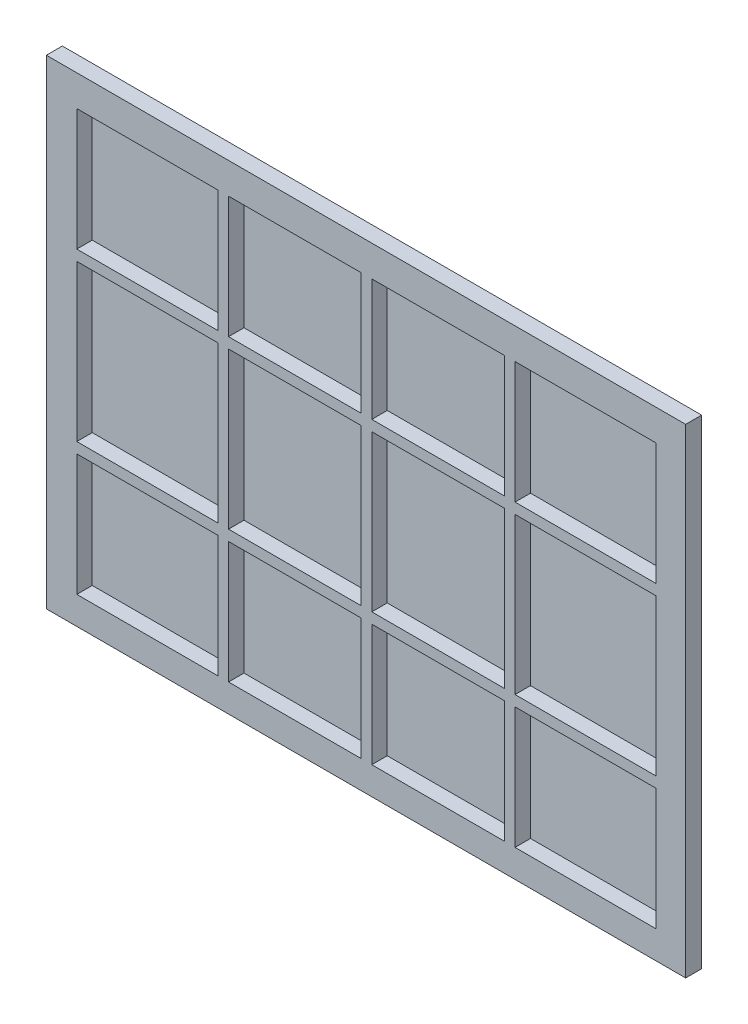
SolidWorks part; units mm, degrees
material "6061 Alloy"
ref_plane "Front Plane" through (0, 0, 0) normal (0, 0, 1) x (1, 0, 0)
ref_plane "Top Plane" through (0, 0, 0) normal (0, 1, 0) x (1, 0, 0)
ref_plane "Right Plane" through (0, 0, 0) normal (1, 0, 0) x (0, 0, -1)
sketch "Sketch2" plane through (0, 0, 0) normal (0, 0, 1) x (1, 0, 0)
  line L1 (0, 0) -> (1200, 0)
  line L2 (0, 0) -> (0, 900)
  line L3 (0, 900) -> (1200, 900)
  line L4 (1200, 0) -> (1200, 900)
  dimension "D1" = 900
  dimension "D2" = 1200
extrude "Boss-Extrude2" add sketch "Sketch2" along normal blind 30 contours L1 L4 L3 L2
sketch "Sketch3" plane through (0, 0, 30) normal (0, 0, 1) x (1, 0, 0)
  line L1 (57.1339, 841.9291) -> (1144.5573, 841.9291)
  line L2 (57.1339, 841.9291) -> (57.1339, 52.1518)
  line L3 (57.1339, 52.1518) -> (1144.5573, 52.1518)
  line L4 (1144.5573, 841.9291) -> (1144.5573, 52.1518)
extrude "Cut-Extrude2" cut sketch "Sketch3" against normal blind 29 contours L2 L3 L4 L1
sketch "Sketch6" plane through (0, 0, 30) normal (0, 0, 1) x (1, 0, 0)
  line L0 (600.8456, 841.9291) -> (600.8456, 52.1518)
  line L1 (57.1339, 841.9291) -> (1144.5573, 841.9291) construction
  line L2 (57.1339, 52.1518) -> (1144.5573, 52.1518) construction
  line L3 (331.9493, 841.9291) -> (331.9493, 52.1518)
  line L4 (57.1339, 603.4738) -> (1144.5573, 603.4738)
  line L5 (869.7419, 841.9291) -> (869.7419, 52.1518)
  line L6 (57.1339, 841.9291) -> (57.1339, 52.1518) construction
  line L7 (1144.5573, 841.9291) -> (1144.5573, 52.1518) construction
  line L8 (57.1339, 290.6071) -> (1144.5573, 290.6071)
rib "Rib6" sketch "Sketch6" sketch "Sketch6" thickness 20 extrusion direction normal to sketch draft on no parameters "D1"=20
sketch "Sketch7" plane through (0, 0, 30) normal (0, 0, 1) x (1, 0, 0)
  circle A0 centre (30.6818, 869.0753) radius 27.4905
  circle A1 centre (1169.3182, 869.0753) radius 27.4905
  circle A2 centre (1169.3182, 30.9247) radius 27.4905
  circle A3 centre (30.6818, 30.9247) radius 27.4905
